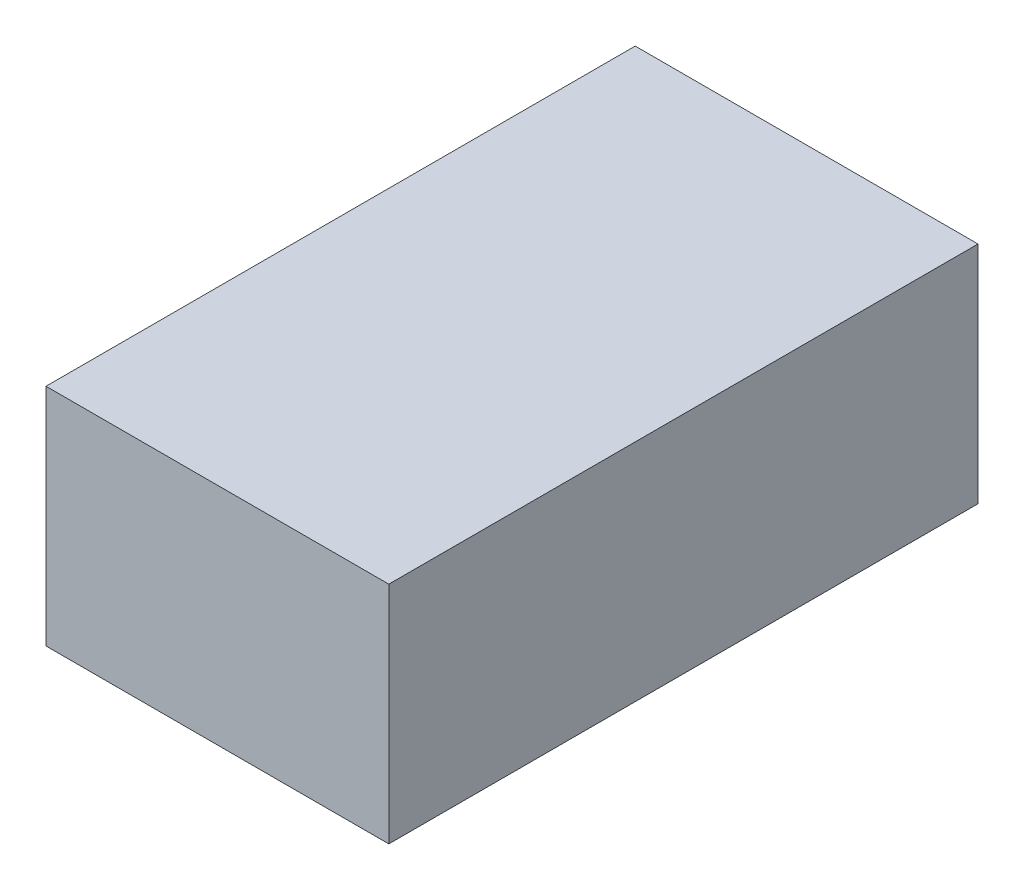
SolidWorks part; units mm, degrees
ref_plane "Front" through (0, 0, 0) normal (0, 0, 1) x (1, 0, 0)
ref_plane "Top" through (0, 0, 0) normal (0, 1, 0) x (1, 0, 0)
ref_plane "Right" through (0, 0, 0) normal (1, 0, 0) x (0, 0, -1)
sketch "Sketch1" plane through (0, 0, 0) normal (0, 1, 0) x (1, 0, 0)
  line L1 (-16, -27.5) -> (16, -27.5)
  line L2 (-16, -27.5) -> (-16, 27.5)
  line L3 (-16, 27.5) -> (16, 27.5)
  line L4 (16, -27.5) -> (16, 27.5)
  line L5 (-16, -27.5) -> (16, 27.5) construction
  line L6 (-16, 27.5) -> (16, -27.5) construction
  point P0 (0, 0)
  dimension "D1" = 32
  dimension "D2" = 55
extrude "Boss-Extrude1" add sketch "Sketch1" along normal blind 21
